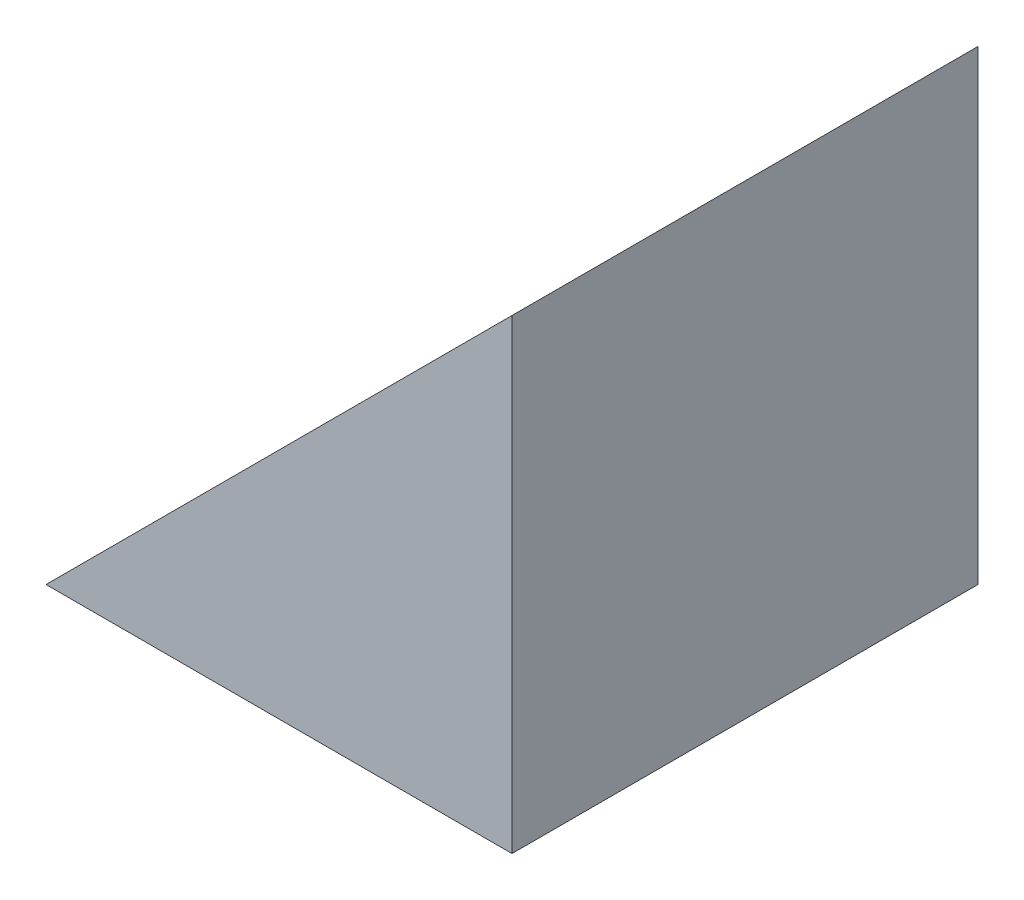
SolidWorks part; units mm, degrees
ref_plane "前视基准面" through (0, 0, 0) normal (0, 0, 1) x (1, 0, 0)
ref_plane "上视基准面" through (0, 0, 0) normal (0, 1, 0) x (1, 0, 0)
ref_plane "右视基准面" through (0, 0, 0) normal (1, 0, 0) x (0, 0, -1)
sketch "草图1" plane through (0, 0, 0) normal (0, 0, 1) x (1, 0, 0)
  line L0 (174.7141, 132.7791) -> (174.7141, 182.7791)
  line L1 (174.7141, 132.7791) -> (124.7141, 132.7791)
  line L2 (124.7141, 132.7791) -> (174.7141, 182.7791)
  dimension "D1" = 50
  dimension "D2" = 50
extrude "凸台-拉伸1" add sketch "草图1" along normal blind 50 contours L2 L0 L1
